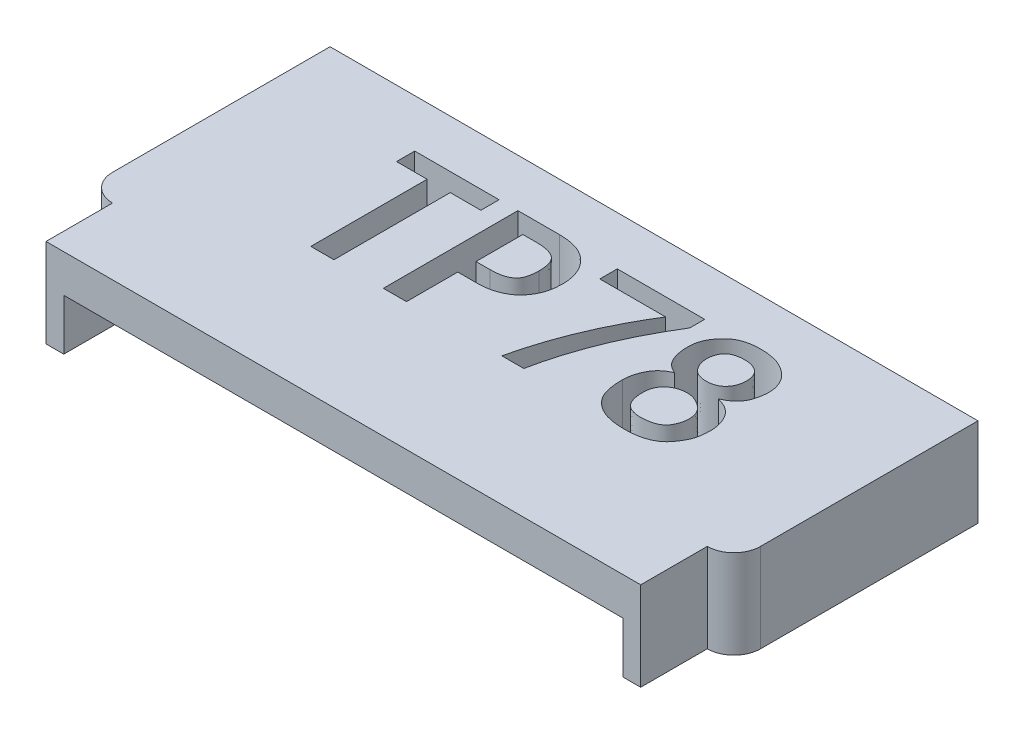
SolidWorks part; units mm, degrees
ref_plane "前视基准面" through (0, 0, 0) normal (0, 0, 1) x (1, 0, 0)
ref_plane "上视基准面" through (0, 0, 0) normal (0, 1, 0) x (1, 0, 0)
ref_plane "右视基准面" through (0, 0, 0) normal (1, 0, 0) x (0, 0, -1)
sketch "草图1" plane through (0, 0, 0) normal (0, 1, 0) x (1, 0, 0)
  line L0 (0.6, -5.5) -> (0.6, -7.0297)
  line L1 (0, 0) -> (14.6, 0)
  line L2 (0, 0) -> (0, -4.9)
  line L3 (0.6, -5.5) -> (14, -5.5)
  line L4 (14.6, 0) -> (14.6, -4.9)
  arc A0 (14, -5.5) -> (14.6, -4.9) centre (14, -4.9) ccw
  arc A1 (0.6, -5.5) -> (0, -4.9) centre (0.6, -4.9) cw
  point P9 (0, -5.5)
  dimension "D3" = 0.6
  dimension "D1" = 5.5
  dimension "D2" = 14.6
extrude "凸台-拉伸1" add sketch "草图1" along normal blind 2 contours A1 L2 L1 L4 A0 L3
sketch "草图2" plane through (0, 0, 5.5) normal (0, 0, 1) x (1, 0, 0)
  line L3 (14, 2) -> (0.6, 2)
  line L4 (14, 2) -> (14, 1.15)
  line L5 (14, 2) -> (14, 0) construction
  line L6 (14, 1.15) -> (0.6, 1.15)
  line L7 (0.6, 2) -> (0.6, 0) construction
  line L8 (0.6, 1.15) -> (0.6, 2)
  dimension "D1" = 0.85
extrude "凸台-拉伸2" add sketch "草图2" along normal blind 1.5
sketch "草图4" plane through (0, 1.15, 0) normal (0, -1, 0) x (1, 0, 0)
  line L0 (13.6, 5.5) -> (13.6, 7)
  line L1 (0.6, 5.5) -> (14, 5.5) construction
  line L2 (0.6, 7) -> (14, 7) construction
  line L3 (13.6, 7) -> (14, 7)
  line L4 (14, 7) -> (14, 5.5)
  line L5 (14, 5.5) -> (13.6, 5.5)
  line L6 (0.6, 7) -> (1, 7)
  line L7 (1, 7) -> (1, 5.5)
  line L8 (1, 5.5) -> (0.6, 5.5)
  line L9 (0.6, 5.5) -> (0.6, 7)
  dimension "D1" = 0.4
extrude "凸台-拉伸3" add sketch "草图4" along normal blind 1.15
sketch "草图5" plane through (0, 2, 0) normal (0, 1, 0) x (1, 0, 0)
  line L0 (0, 0) -> (0, -4.9) construction
  line L1 (0, 0) -> (14.6, 0) construction
  text T0 "TP78" font "黑体" height in points 10
  point P3 (0, 0)
  point P5 (2.49, -0.1695)
  dimension "D1" = 2.8
  dimension "D2" = 4.2
extrude "切除-拉伸2" cut sketch "草图5" against normal blind 1.9
